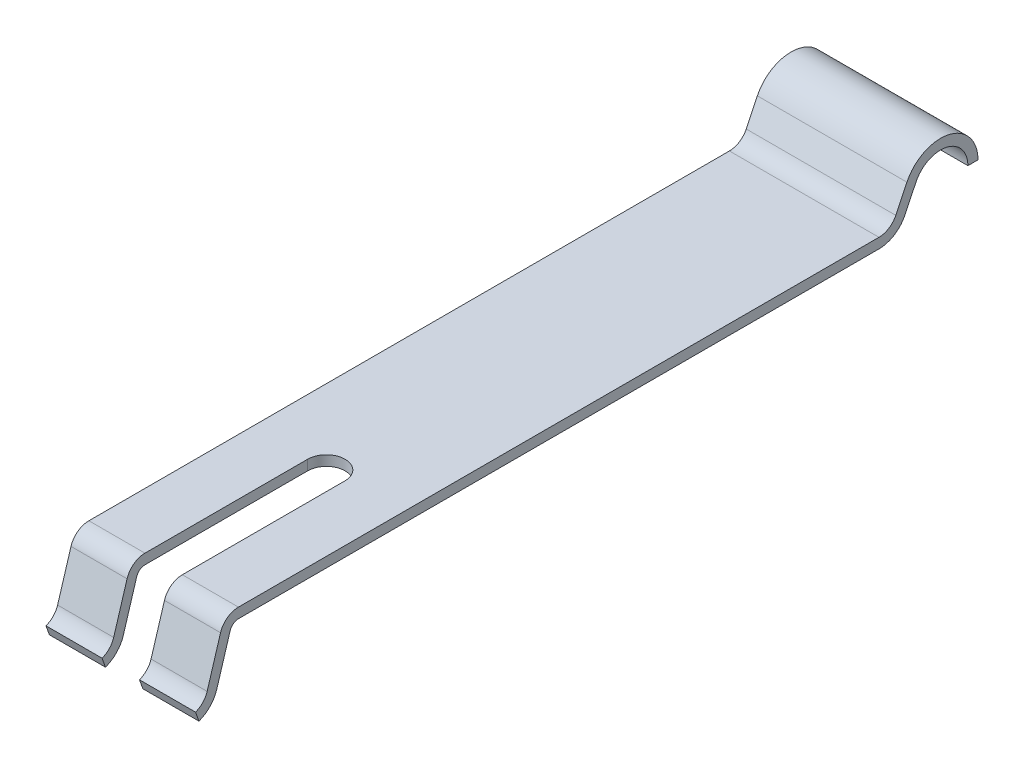
SolidWorks part; units mm, degrees
ref_plane "Front Plane" through (0, 0, 0) normal (0, 0, 1) x (1, 0, 0)
ref_plane "Top Plane" through (0, 0, 0) normal (0, 1, 0) x (1, 0, 0)
ref_plane "Right Plane" through (0, 0, 0) normal (1, 0, 0) x (0, 0, -1)
sketch "Sketch1" plane through (0, 0, 0) normal (1, 0, 0) x (0, 0, -1)
  line L0 (-9.0352, 0) -> (8.0979, 0)
  line L1 (-9.5136, -0.3546) -> (-9.8721, -1.5341)
  line L2 (-9.2552, -0.4331) -> (-9.6138, -1.6126)
  line L3 (8.5485, 0.2833) -> (8.8462, 0.9025)
  line L4 (-9.0352, -0.27) -> (8.0979, -0.27)
  line L5 (8.7918, 0.1663) -> (9.0896, 0.7855)
  line L6 (-10.0917, -2.1138) -> (-10.1825, -1.8595)
  line L7 (10.4775, 0.4692) -> (10.7475, 0.4692)
  arc A0 (10.7475, 0.4692) -> (8.8462, 0.9025) centre (9.7475, 0.4692) ccw
  arc A1 (8.0979, 0) -> (8.5485, 0.2833) centre (8.0979, 0.5) ccw
  arc A2 (-9.0352, 0) -> (-9.5136, -0.3546) centre (-9.0352, -0.5) ccw
  arc A3 (-10.1825, -1.8595) -> (-9.8721, -1.5341) centre (-10.3505, -1.3886) ccw
  arc A5 (-10.0917, -2.1138) -> (-9.6138, -1.6126) centre (-10.3505, -1.3886) ccw
  arc A6 (-9.0352, -0.27) -> (-9.2552, -0.4331) centre (-9.0352, -0.5) ccw
  arc A7 (8.0979, -0.27) -> (8.7918, 0.1663) centre (8.0979, 0.5) ccw
  arc A8 (10.4775, 0.4692) -> (9.0896, 0.7855) centre (9.7475, 0.4692) ccw
  point P8 (-9.4021, 0)
  point P11 (8.5979, 0)
  dimension "D4" = 8.0979
  dimension "D5" = 8.5485
  dimension "D2" = 0.5
  dimension "D3" = 0.77
  dimension "D15" = 9.4021
  dimension "D1" = 1
  dimension "D6" = 8.5979
  dimension "D7" = 8.8462
  dimension "D8" = 9.0352
  dimension "D9" = 9.2552
  dimension "D10" = 9.6138
  dimension "D11" = 10.0917
extrude "Boss-Extrude1" add sketch "Sketch1" along normal blind 4
sketch "Sketch2" plane through (0, 0, 0) normal (0, 1, 0) x (1, 0, 0)
  line L0 (4, -10.1825) -> (0, -10.1825) construction
  line L2 (1.5, -4.6825) -> (1.5, -10.1825)
  line L3 (1.5, -10.1825) -> (2.5, -10.1825)
  line L4 (2.5, -4.6825) -> (2.5, -10.1825)
  line L5 (4, 8.0979) -> (4, -9.0352) construction
  arc A0 (2.5, -4.6825) -> (1.5, -4.6825) centre (2, -4.6825) ccw
  dimension "D1" = 5.5
  dimension "D2" = 0.5
  dimension "D3" = 1.5
extrude "Cut-Extrude1" cut sketch "Sketch2" against normal blind 4.15
ref_plane "Plane1" through (2, 0, 0) normal (1, 0, 0) x (0, 0, -1)
